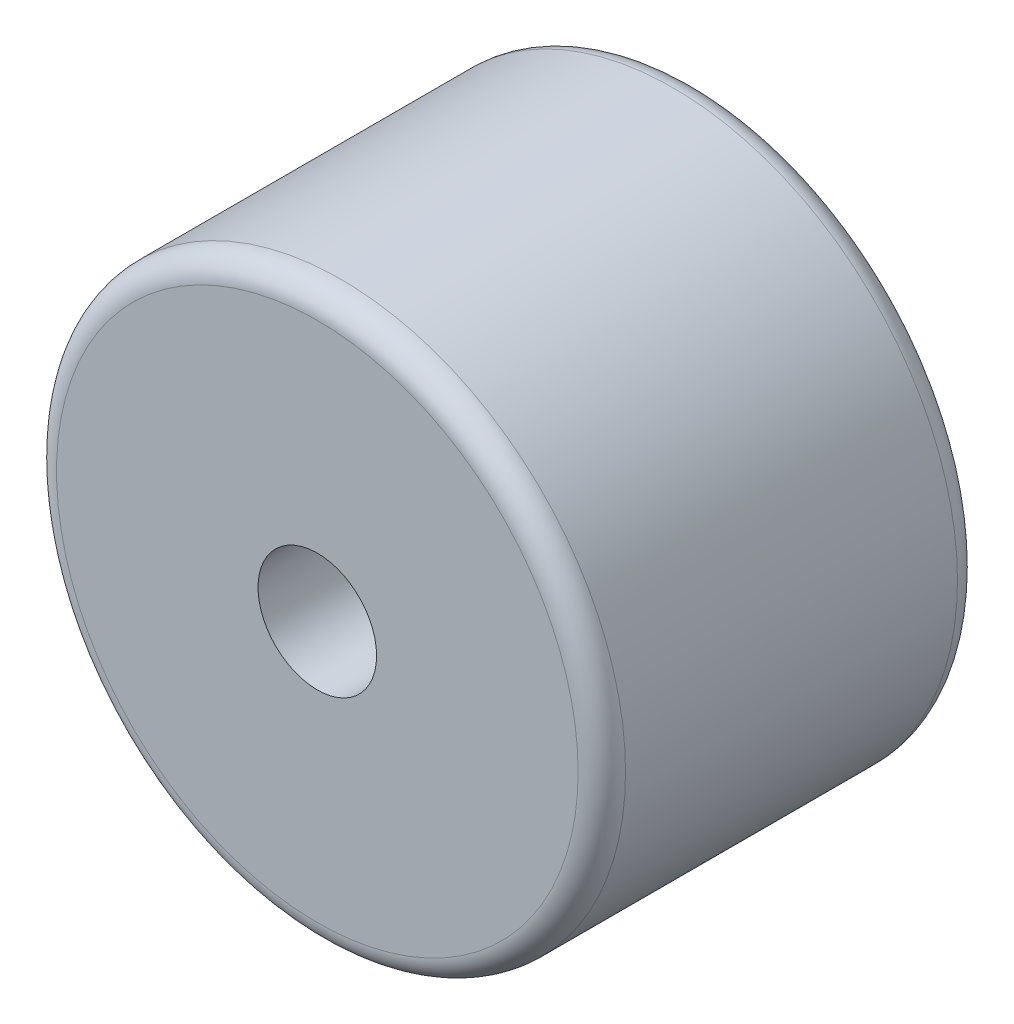
SolidWorks part; units mm, degrees
material "ABS"
ref_plane "Front Plane" through (0, 0, 0) normal (0, 0, 1) x (1, 0, 0)
ref_plane "Top Plane" through (0, 0, 0) normal (0, 1, 0) x (1, 0, 0)
ref_plane "Right Plane" through (0, 0, 0) normal (1, 0, 0) x (0, 0, -1)
sketch "Sketch1" plane through (0, 0, 0) normal (0, 0, 1) x (1, 0, 0)
  circle A0 centre (0, 0) radius 12
  dimension "D1" = 24
extrude "Boss-Extrude1" add sketch "Sketch1" along normal blind 16
sketch "Sketch2" plane through (0, 0, 16) normal (0, 0, 1) x (1, 0, 0)
  circle A0 centre (0, 0) radius 2.5
  dimension "D1" = 5
extrude "Cut-Extrude1" cut sketch "Sketch2" against normal blind 30
fillet "Fillet2" radius 1 2 edges at (12, 0, 0) (12, 0, 16)
